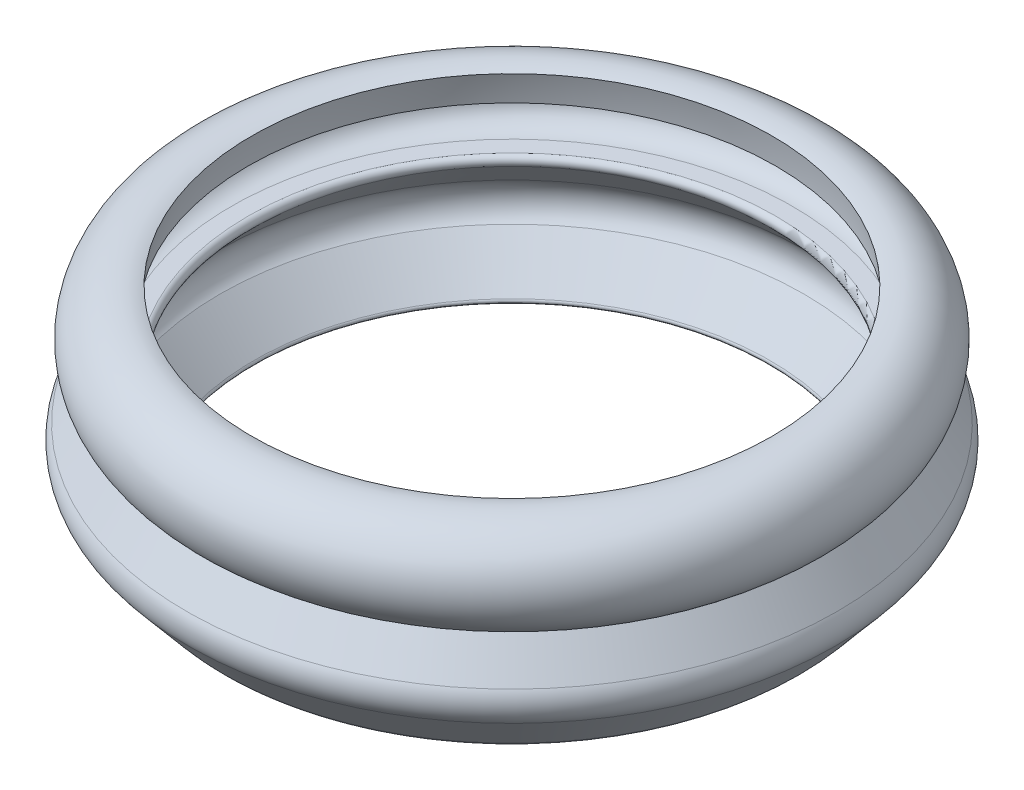
SolidWorks part; units mm, degrees
ref_plane "Front Plane" through (0, 0, 0) normal (0, 0, 1) x (1, 0, 0)
ref_plane "Top Plane" through (0, 0, 0) normal (0, 1, 0) x (1, 0, 0)
ref_plane "Right Plane" through (0, 0, 0) normal (1, 0, 0) x (0, 0, -1)
sketch "Sketch1" plane through (0, 0, 0) normal (0, 0, 1) x (1, 0, 0)
  line L0 (-2.4542, -2.3627) -> (7.5413, -2.3627) construction
  line L1 (2.5436, -2.3627) -> (2.5436, 2.6704) construction
  line L2 (2.5436, 2.2909) -> (2.5436, 2.6704) construction
  line L3 (-2.7542, -1.9545) -> (-2.4388, -1.9545) construction
  line L4 (-2.4542, -2.7709) -> (-2.7542, -2.7709) construction
  line L5 (-2.7542, -1.9545) -> (-2.4388, -1.9545)
  line L6 (-3.1958, -3.0255) -> (-3.6054, -3.6747)
  line L7 (-2.8939, -5.0617) -> (-3.5652, -4.2633)
  line L8 (-2.9722, -4.316) -> (-2.3292, -5.0812)
  line L9 (-2.9944, -3.6092) -> (-2.3722, -2.9467)
  line L10 (-2.7542, -2.7709) -> (-2.4362, -2.7709)
  line L19 (-2.6633, -5.1686) -> (-2.3633, -5.1676)
  arc A0 (-2.7542, -1.9545) -> (-2.7542, -2.7709) centre (-2.7542, -2.3627) ccw construction
  arc A1 (-2.0542, -2.3615) -> (-2.4542, -2.7709) centre (-2.4624, -2.3628) cw construction
  arc A2 (-2.0542, -2.3615) -> (2.5436, 2.2909) centre (2.6431, -2.4055) cw construction
  arc A3 (-2.4388, -1.9545) -> (2.5436, 2.6704) centre (2.5471, -2.3296) cw construction
  arc A4 (-3.6054, -3.6747) -> (-3.5652, -4.2633) centre (-3.1825, -3.9415) ccw
  arc A5 (-2.4388, -1.9545) -> (-2.3712, -1.429) centre (2.5471, -2.3296) cw
  arc A6 (-2.7542, -2.7709) -> (-2.7542, -1.9545) centre (-2.7542, -2.3627) cw
  arc A7 (-2.9722, -4.316) -> (-2.9944, -3.6092) centre (-2.6299, -3.9515) cw
  arc A8 (-3.1958, -3.0255) -> (-2.3712, -1.429) centre (-2.6546, -2.2938) cw
  arc A10 (-2.4362, -2.7709) -> (-2.3722, -2.9467) centre (-2.4538, -2.8769) cw
  arc A11 (-2.3633, -5.1676) -> (-2.3292, -5.0812) centre (-2.3635, -5.1176) ccw
  arc A12 (-2.8939, -5.0617) -> (-2.6633, -5.1686) centre (-2.6643, -4.8686) ccw
  dimension "D2" = 0.5
  dimension "D3" = 0.5
  dimension "D4" = 0.05
  dimension "D5" = 0.3
revolve "Revolve1" add sketch "Sketch1" angle 360 about L1
